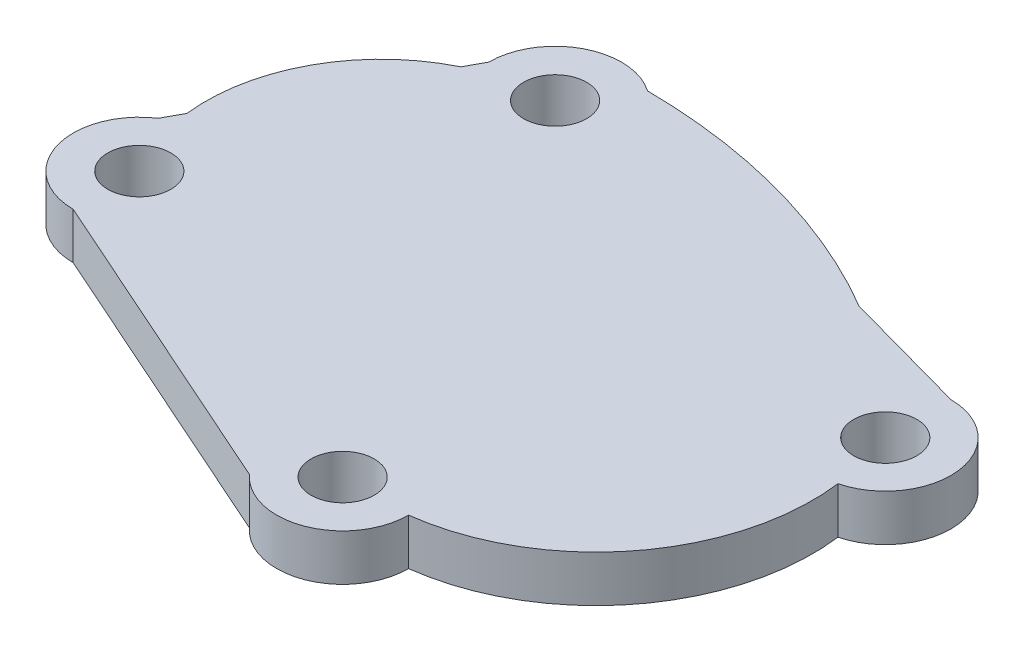
SolidWorks part; units mm, degrees
ref_plane "Front" through (0, 0, 0) normal (0, 0, 1) x (1, 0, 0)
ref_plane "Top" through (0, 0, 0) normal (0, 1, 0) x (1, 0, 0)
ref_plane "Right" through (0, 0, 0) normal (1, 0, 0) x (0, 0, -1)
sketch "Sketch1" plane through (0, 0, 0) normal (0, 1, 0) x (1, 0, 0)
  line L0 (0, 0) -> (50.2408, -22.3799) construction
  line L1 (50.2408, -22.3799) -> (82.7353, 19.4903) construction
  line L2 (82.7353, 19.4903) -> (20.1036, 36.8761) construction
  line L3 (20.1036, 36.8761) -> (0, 0) construction
  line L4 (0, 0) -> (82.7353, 19.4903) construction
  line L5 (0, -9.0551) -> (43.5503, -28.4547)
  line L7 (65.3666, 33.2853) -> (82.7353, 28.4903)
  line L8 (11.0026, 36.8761) -> (9.6591, 34.4117)
  line L9 (-3.5872, 10.114) -> (-4.977, 7.5647)
  circle A0 centre (20.1036, 36.8761) radius 4.325
  circle A1 centre (0, 0) radius 4.325
  circle A2 centre (50.2408, -22.3799) radius 4.325
  circle A3 centre (82.7353, 19.4903) radius 4.325
  arc A4 (25.3023, 44.3461) -> (11.0026, 36.8761) centre (20.1036, 36.8761) ccw
  arc A5 (-4.977, 7.5647) -> (0, -9.0551) centre (0, 0) ccw
  arc A6 (84.9692, 10.7719) -> (82.7353, 28.4903) centre (82.7353, 19.4903) ccw
  arc A7 (43.5503, -28.4547) -> (59.2778, -22.3799) centre (50.2408, -22.3799) ccw
  arc A8 (25.3023, 44.3461) -> (65.3666, 33.2853) centre (24.7757, -35.6521) cw
  arc A9 (9.6591, 34.4117) -> (-3.5872, 10.114) centre (20.2532, 12.8766) ccw
  arc A10 (84.9692, 10.7719) -> (59.2778, -22.3799) centre (55.5476, 7.0417) cw
  dimension "D1" = 53
  dimension "D2" = 55
  dimension "D3" = 65
  dimension "D4" = 42
  dimension "D5" = 85
extrude "Extrude1" add sketch "Sketch1" along normal blind 6.35
